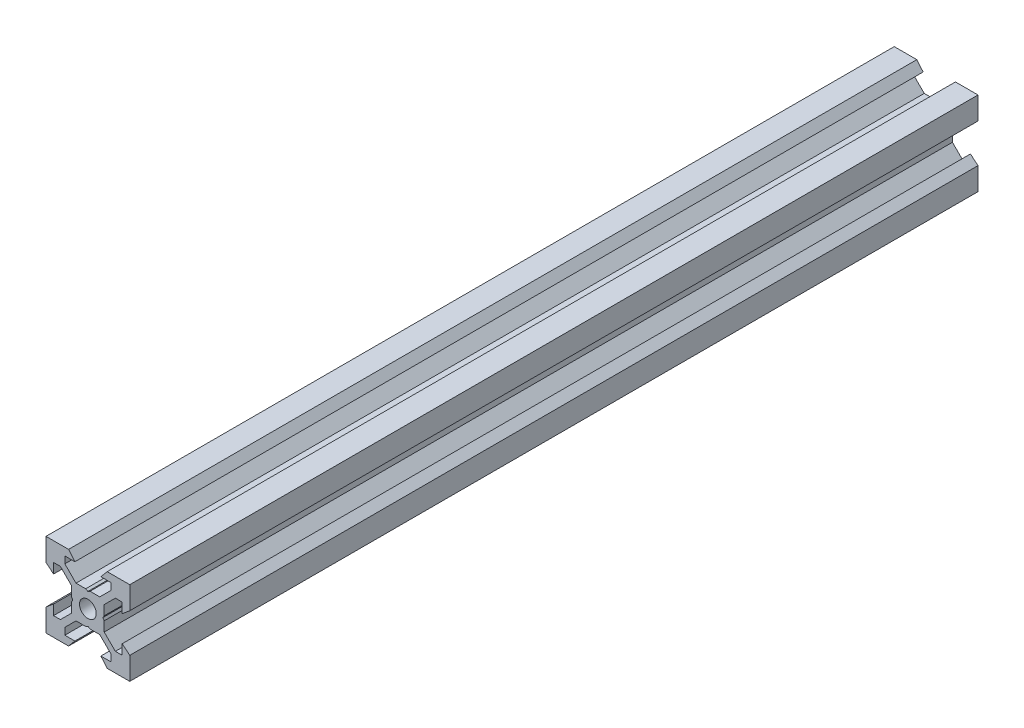
SolidWorks part; units mm, degrees
ref_plane "Front Plane" through (0, 0, 0) normal (0, 0, 1) x (1, 0, 0)
ref_plane "Top Plane" through (0, 0, 0) normal (0, 1, 0) x (1, 0, 0)
ref_plane "Right Plane" through (0, 0, 0) normal (1, 0, 0) x (0, 0, -1)
sketch "Sketch1" plane through (0, 0, 0) normal (0, 0, 1) x (1, 0, 0)
  line L0 (10, 10) -> (4.6104, 10) construction
  line L1 (10, 10) -> (10, 4.6104) construction
  line L2 (10, -10) -> (10, -4.6104) construction
  line L3 (10, -10) -> (4.6104, -10) construction
  line L4 (10, 10) -> (10, 4.6104)
  line L5 (6.5607, 5.5) -> (8.2, 5.5)
  line L6 (5.5, 8.2) -> (5.5, 6.5607)
  line L7 (10, 10) -> (4.6104, 10)
  line L8 (10, 10) -> (10, 4.6104)
  line L9 (6.5607, 5.5) -> (3.9, 2.8393)
  line L10 (5.5, 6.5607) -> (2.8393, 3.9)
  line L11 (10, 4.6104) -> (8.2, 3.1)
  line L12 (4.6104, 10) -> (3.1, 8.2)
  line L13 (8.2, 3.1) -> (8.2, 5.5)
  line L14 (3.1, 8.2) -> (5.5, 8.2)
  line L15 (-6.5607, 5.5) -> (-8.2, 5.5)
  line L16 (6.5607, -5.5) -> (8.2, -5.5)
  line L17 (3.1, -8.2) -> (5.5, -8.2)
  line L18 (8.2, -3.1) -> (8.2, -5.5)
  line L19 (4.6104, -10) -> (3.1, -8.2)
  line L20 (10, -4.6104) -> (8.2, -3.1)
  line L21 (0.5196, -3.9) -> (0, -3.6)
  line L22 (0.5196, 3.9) -> (0, 3.6)
  line L23 (3.6, 0) -> (3.9, -0.5196)
  line L24 (3.9, 0.5196) -> (3.6, 0)
  line L25 (3.9, 0.5196) -> (3.9, 2.8393)
  line L26 (2.8393, 3.9) -> (0.5196, 3.9)
  line L27 (3.9, -2.8393) -> (3.9, -0.5196)
  line L28 (2.8393, -3.9) -> (0.5196, -3.9)
  line L29 (5.5, -6.5607) -> (2.8393, -3.9)
  line L30 (6.5607, -5.5) -> (3.9, -2.8393)
  line L31 (10, -10) -> (10, -4.6104)
  line L32 (10, -10) -> (4.6104, -10)
  line L33 (5.5, -8.2) -> (5.5, -6.5607)
  line L34 (-6.5607, -5.5) -> (-8.2, -5.5)
  line L35 (10, -10) -> (10, -4.6104)
  line L36 (0, 0) -> (0, 8.2) construction
  line L37 (-10, -10) -> (-4.6104, -10) construction
  line L38 (-10, -10) -> (-10, -4.6104) construction
  line L39 (-10, 10) -> (-10, 4.6104) construction
  line L40 (-10, 10) -> (-4.6104, 10) construction
  line L41 (-10, -10) -> (-10, -4.6104)
  line L43 (-5.5, -8.2) -> (-5.5, -6.5607)
  line L44 (-10, -10) -> (-4.6104, -10)
  line L45 (-10, -10) -> (-10, -4.6104)
  line L46 (-6.5607, -5.5) -> (-3.9, -2.8393)
  line L47 (-5.5, -6.5607) -> (-2.8393, -3.9)
  line L48 (-2.8393, -3.9) -> (-0.5196, -3.9)
  line L49 (-3.9, -2.8393) -> (-3.9, -0.5196)
  line L50 (-2.8393, 3.9) -> (-0.5196, 3.9)
  line L51 (-3.9, 0.5196) -> (-3.9, 2.8393)
  line L52 (-3.9, 0.5196) -> (-3.6, 0)
  line L53 (-3.6, 0) -> (-3.9, -0.5196)
  line L54 (-0.5196, 3.9) -> (0, 3.6)
  line L55 (-0.5196, -3.9) -> (0, -3.6)
  line L56 (-10, -4.6104) -> (-8.2, -3.1)
  line L57 (-4.6104, -10) -> (-3.1, -8.2)
  line L58 (-8.2, -3.1) -> (-8.2, -5.5)
  line L59 (-3.1, -8.2) -> (-5.5, -8.2)
  line L60 (-10, -10) -> (10, -10) construction
  line L61 (-10, -10) -> (-10, 10) construction
  line L62 (-3.1, 8.2) -> (-5.5, 8.2)
  line L63 (-8.2, 3.1) -> (-8.2, 5.5)
  line L64 (-4.6104, 10) -> (-3.1, 8.2)
  line L65 (-10, 4.6104) -> (-8.2, 3.1)
  line L66 (-5.5, 6.5607) -> (-2.8393, 3.9)
  line L67 (-6.5607, 5.5) -> (-3.9, 2.8393)
  line L68 (-10, 10) -> (-10, 4.6104)
  line L69 (-10, 10) -> (-4.6104, 10)
  line L70 (-5.5, 8.2) -> (-5.5, 6.5607)
  line L71 (-10, 10) -> (10, 10) construction
  line L72 (-10, 10) -> (-10, 4.6104)
  line L73 (10, -10) -> (10, 10) construction
  line L74 (-10, -10) -> (10, 10) construction
  line L75 (-10, 10) -> (10, -10) construction
  circle A0 centre (0, 0) radius 2
  dimension "D7" = 4
  dimension "D1" = 20
  dimension "D2" = 5.3896
  dimension "D3" = 4.5
  dimension "D4" = 50
  dimension "D5" = 1.8
  dimension "D6" = 1.5104
  dimension "D8" = 5.5
  dimension "D9" = 120
  dimension "D10" = 0.3
  dimension "D11" = 2.3197
  dimension "D12" = 7.8
  dimension "D13" = 7.8
  dimension "D14" = 1.5
  dimension "D15" = 2.6607
extrude "Boss-Extrude1" add sketch "Sketch1" along normal mid plane 202.56 contours L70 L62 L64 L69 L68 L65 L63 L15 L67 L51 L52 L53 L49 L46 L34 L58 L56 L41 L44 L57 L59 L43 L47 L48 L55 L21 L28 L29 L33 L17 L19 L32 L31 L20 L18 L16 L30 L27 L23 L24 L25 L9 L5 L13 L11 L4 L7 L12 L14 L6 L10
